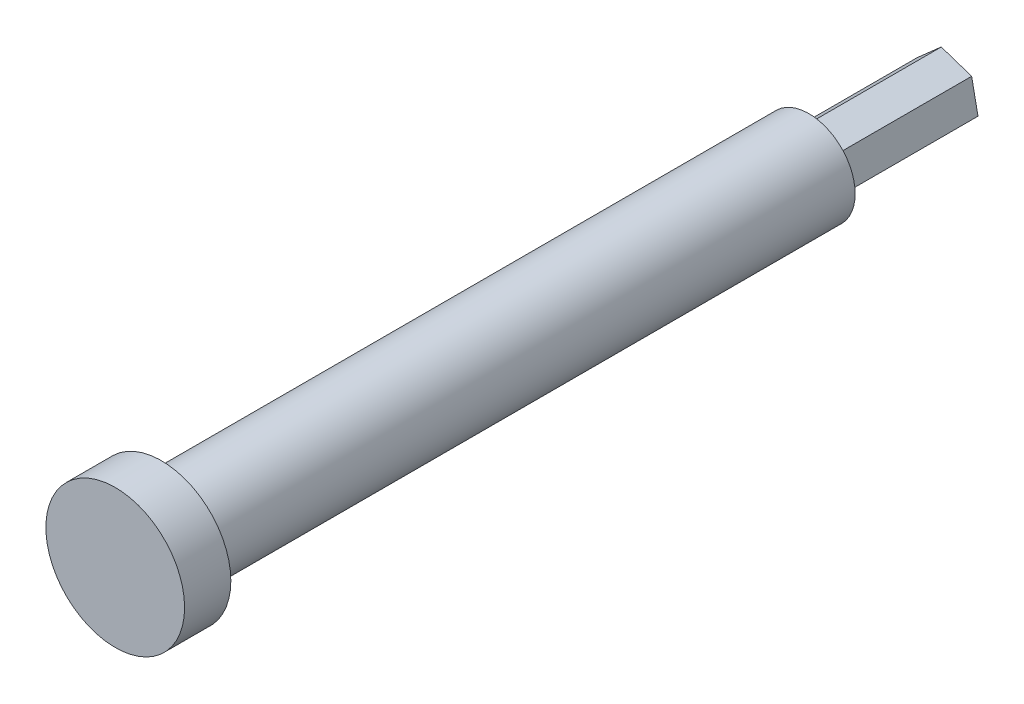
SolidWorks part; units mm, degrees
ref_plane "Plan de face" through (0, 0, 0) normal (0, 0, 1) x (1, 0, 0)
ref_plane "Plan de dessus" through (0, 0, 0) normal (0, 1, 0) x (1, 0, 0)
ref_plane "Plan de droite" through (0, 0, 0) normal (1, 0, 0) x (0, 0, -1)
sketch "Esquisse1" plane through (0, 0, 0) normal (0, 0, 1) x (1, 0, 0)
  line L1 (-0.6866, 3.3954) -> (-3.2838, 1.103)
  line L2 (-3.2838, 1.103) -> (-2.5971, -2.2923)
  line L3 (-2.5971, -2.2923) -> (0.6866, -3.3954)
  line L4 (0.6866, -3.3954) -> (3.2838, -1.103)
  line L5 (3.2838, -1.103) -> (2.5971, 2.2923)
  line L6 (2.5971, 2.2923) -> (-0.6866, 3.3954)
  circle A0 centre (0, 0) radius 3 construction
  dimension "D1" = 6
extrude "Boss.-Extru.1" add sketch "Esquisse1" along normal blind 15
sketch "Esquisse2" plane through (0, 0, 15) normal (0, 0, 1) x (1, 0, 0)
  circle A0 centre (0, 0) radius 5
  dimension "D1" = 10
extrude "Boss.-Extru.2" add sketch "Esquisse2" along normal blind 70
sketch "Esquisse3" plane through (0, 0, 85) normal (0, 0, 1) x (1, 0, 0)
  circle A0 centre (0, 0) radius 7.5
  dimension "D1" = 15
extrude "Boss.-Extru.3" add sketch "Esquisse3" along normal blind 5
